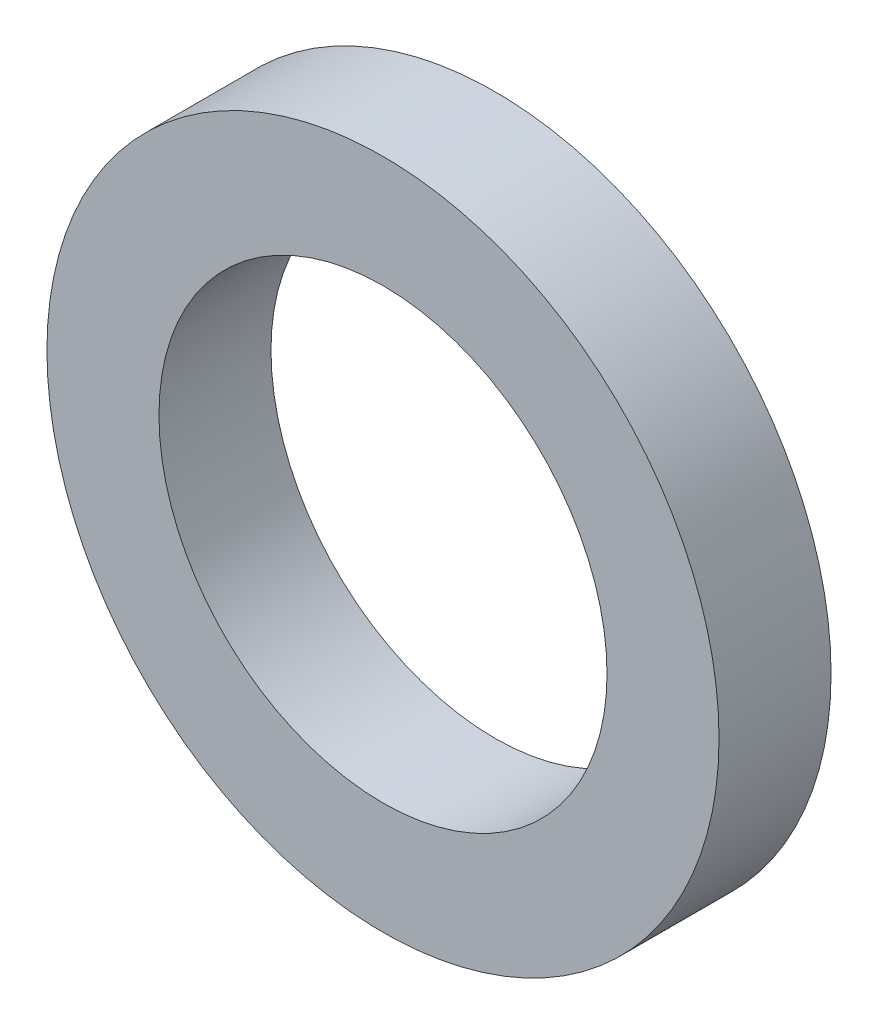
SolidWorks part; units mm, degrees
ref_plane "Front Plane" through (0, 0, 0) normal (0, 0, 1) x (1, 0, 0)
ref_plane "Top Plane" through (0, 0, 0) normal (0, 1, 0) x (1, 0, 0)
ref_plane "Right Plane" through (0, 0, 0) normal (1, 0, 0) x (0, 0, -1)
sketch "Sketch1" plane through (0, 0, 0) normal (0, 0, 1) x (1, 0, 0)
  circle A1 centre (0, 0) radius 15
  circle A2 centre (0, 0) radius 10
  dimension "D1" = 20
  dimension "D2" = 30
extrude "Boss-Extrude1" add sketch "Sketch1" along normal blind 5
